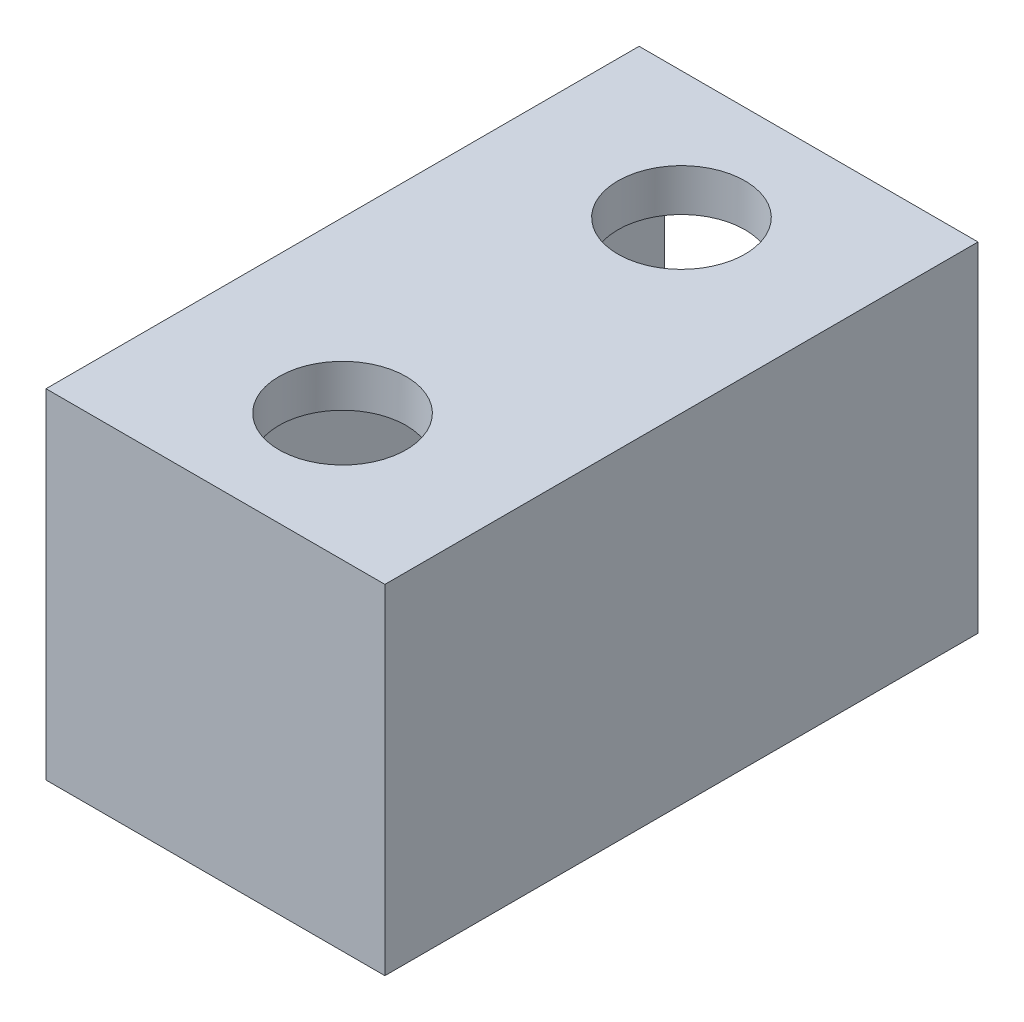
SolidWorks part; units mm, degrees
ref_plane "Front Plane" through (0, 0, 0) normal (0, 0, 1) x (1, 0, 0)
ref_plane "Top Plane" through (0, 0, 0) normal (0, 1, 0) x (1, 0, 0)
ref_plane "Right Plane" through (0, 0, 0) normal (1, 0, 0) x (0, 0, -1)
sketch "Sketch1" plane through (0, 0, 0) normal (0, 0, 1) x (1, 0, 0)
  line L1 (0, 0) -> (-40, 0)
  line L2 (0, 0) -> (0, 40)
  line L3 (0, 40) -> (-40, 40)
  line L4 (-40, 0) -> (-40, 40)
  line L5 (-37, 37) -> (-3, 37)
  line L6 (-37, 37) -> (-37, 3)
  line L7 (-37, 3) -> (-3, 3)
  line L8 (-3, 37) -> (-3, 3)
  dimension "D1" = 40
  dimension "D2" = 40
  dimension "D3" = 3
  dimension "D4" = 3
  dimension "D5" = 3
  dimension "D6" = 3
extrude "Boss-Extrude1" add sketch "Sketch1" along normal blind 70
sketch "Sketch2" plane through (0, 37, 0) normal (0, -1, 0) x (-1, 0, 0)
  line L0 (37, -70) -> (37, 0) construction
  line L1 (3, -70) -> (37, -70)
  line L2 (3, -70) -> (3, -67)
  line L3 (3, -67) -> (37, -67)
  line L4 (37, -70) -> (37, -67)
  dimension "D1" = 3
extrude "Boss-Extrude2" add sketch "Sketch2" along normal blind 37
sketch "Sketch3" plane through (0, 40, 0) normal (0, 1, 0) x (1, 0, 0)
  line L0 (-20, 0) -> (-20, -70)
  line L1 (0, 0) -> (-40, 0) construction
  line L2 (0, -70) -> (-40, -70) construction
  line L4 (-9.4505, -15) -> (-30.5495, -15)
  line L5 (-9.4505, -15) -> (-9.4505, -55)
  line L6 (-9.4505, -55) -> (-30.5495, -55)
  line L7 (-30.5495, -15) -> (-30.5495, -55)
  line L8 (-9.4505, -15) -> (-30.5495, -55) construction
  line L9 (-9.4505, -55) -> (-30.5495, -15) construction
  circle A0 centre (-20, -15) radius 7.5
  circle A1 centre (-20, -55) radius 7.5
  point P6 (-20, -35)
  dimension "D2" = 15
  dimension "D3" = 15
  dimension "D1" = 40
extrude "Cut-Extrude1" cut sketch "Sketch3" against normal blind 37 contours L0 A0 L4 | L4 A0 L0 | L0 A0 L4 | L4 A0 L0 | L0 A1 L6 | L6 A1 L0 | L0 A1 L6 | L6 A1 L0
sketch "Sketch4" plane through (0, 37, 0) normal (0, -1, 0) x (-1, 0, 0)
  circle A0 centre (20, -15) radius 8.5
  circle A1 centre (20, -55) radius 8.5
  circle A2 centre (20, -15) radius 7.5
  circle A3 centre (20, -55) radius 7.5
  dimension "D1" = 17
  dimension "D2" = 17
extrude "Boss-Extrude3" add sketch "Sketch4" along normal blind 2
sketch "Sketch6" plane through (0, 3, 0) normal (0, 1, 0) x (1, 0, 0)
  circle A0 centre (-20, -15) radius 7.5
  circle A1 centre (-20, -55) radius 7.5
extrude "Boss-Extrude4" add sketch "Sketch6" against normal blind 10
fillet "Fillet2" radius 1.5 1 edges at (-20, -7, 62.5)
fillet "Fillet3" radius 1.5 1 edges at (-20, -7, 22.5)
fillet "Fillet4" radius 1.5 1 edges at (-27.5, 0, 15)
fillet "Fillet5" radius 1.5 1 edges at (-27.5, 0, 55)
